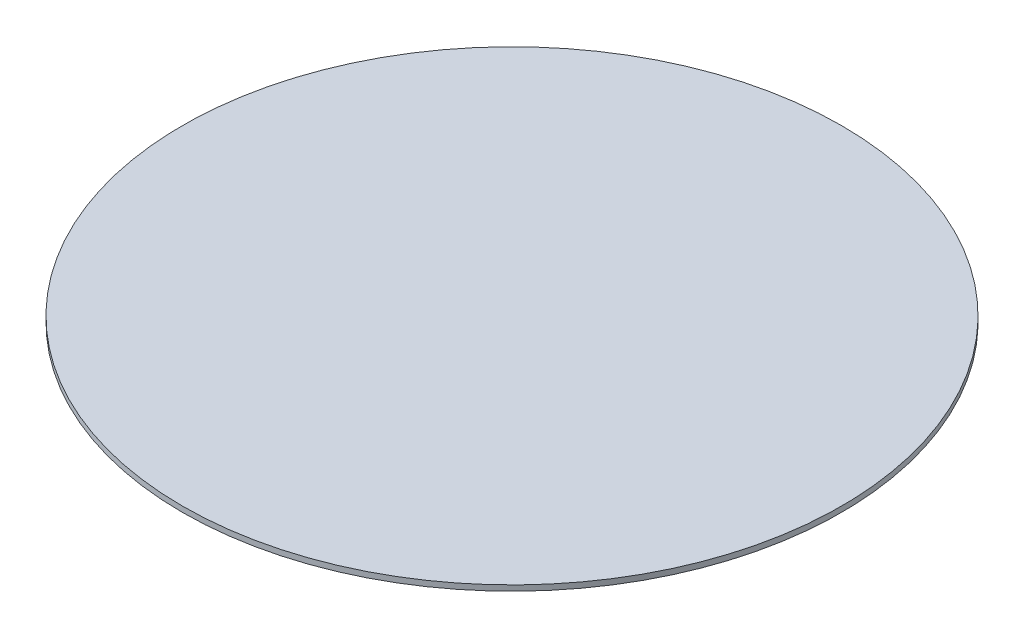
SolidWorks part; units mm, degrees
ref_plane "Ebene vorne" through (0, 0, 0) normal (0, 0, 1) x (1, 0, 0)
ref_plane "Ebene oben" through (0, 0, 0) normal (0, 1, 0) x (1, 0, 0)
ref_plane "Ebene rechts" through (0, 0, 0) normal (1, 0, 0) x (0, 0, -1)
sketch "Skizze1" plane through (0, 0, 0) normal (0, 1, 0) x (1, 0, 0)
  circle A0 centre (0, 0) radius 1200
  dimension "Breite" = 2400
extrude "Aufsatz-Linear austragen1" add sketch "Skizze1" along normal blind 20
equation "\"Staerke@Aufsatz-Linear austragen1\" = ( if ( \"Breite@Skizze1\" = 1600 , 12 , 1000 ) )"
equation "\"Staerke@Aufsatz-Linear austragen1\" = ( iif ( \"Breite@Skizze1\" = 1600 , 12 , iif ( \"Breite@Skizze1\" = 1200 , 12 , iif ( \"Breite@Skizze1\" = 2000 , 16 , iif ( \"Breite@Skizze1\" = 1400 , 16 , iif ( \"Breite@Skizze1\" = 2400 , 20 , iif ( \"Breite@Skizze1\" = 1700 , 20 , 10000 ) ) ) ) ) ) )"
